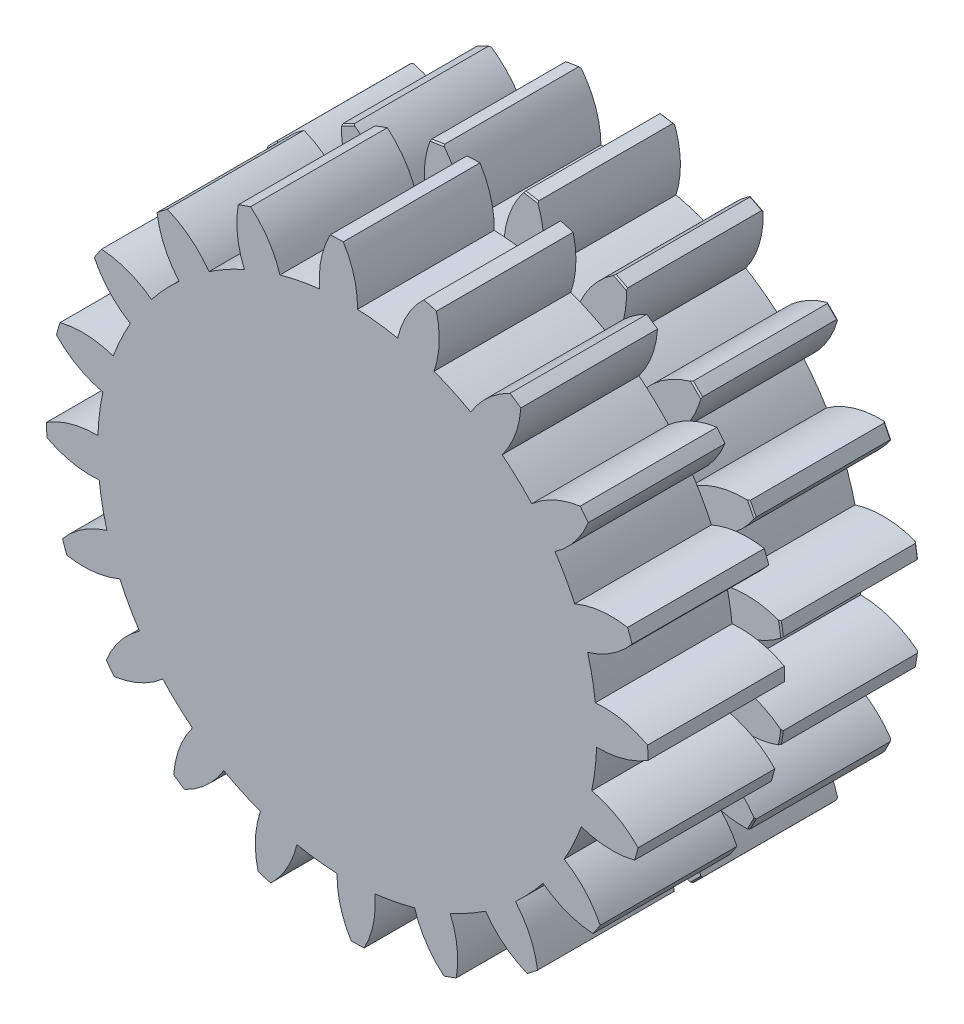
SolidWorks part; units mm, degrees
ref_plane "Front Plane" through (0, 0, 0) normal (0, 0, 1) x (1, 0, 0)
ref_plane "Top Plane" through (0, 0, 0) normal (0, 1, 0) x (1, 0, 0)
ref_plane "Right Plane" through (0, 0, 0) normal (1, 0, 0) x (0, 0, -1)
sketch "Sketch2" plane through (0, 0, 0) normal (0, 0, 1) x (1, 0, 0)
  circle A0 centre (0, 0) radius 20 construction
  circle A1 centre (0, 0) radius 22
  dimension "pitch cirlcle" = 40
  dimension "pitch circle 2" = 44
extrude "Boss-Extrude1" add sketch "Sketch2" along normal mid plane 10
sketch "Sketch3" plane through (0, 0, 5) normal (0, 0, 1) x (1, 0, 0)
  line L0 (0, 0) -> (0, 22) construction
  line L1 (6.7984, 20.9232) -> (0, 0) construction
  line L2 (0, 0) -> (3.4416, 21.7291) construction
  line L3 (0, 0) -> (-1.1551, 17.9629) construction
  line L4 (-1.5692, 19.9383) -> (1.5692, 19.9383) construction
  line L5 (1.5692, 19.9383) -> (4.6689, 19.4474) construction
  line L6 (0, 15.6271) -> (-2.2766, 21.8819) construction
  arc A0 (1.1551, 17.9629) -> (-1.1551, 17.9629) centre (0, 0) ccw
  circle A2 centre (0, 0) radius 22 construction
  circle A3 centre (0, 0) radius 19.75 construction
  arc A4 (-2.6166, 21.8438) -> (-1.1551, 17.9629) centre (-8.2502, 17.5067) cw
  arc A5 (2.6166, 21.8438) -> (1.1551, 17.9629) centre (8.2502, 17.5067) ccw
  circle A6 centre (0, 0) radius 20 construction
  circle A7 centre (0, 0) radius 22 construction
  arc A8 (2.6166, 21.8438) -> (-2.6166, 21.8438) centre (0, 0) ccw
  dimension "angle displacement" = 18
  dimension "dedenum" = 4
  dimension "addendum" = 2.25
  dimension "Pressure Angle" = 20
extrude "Cut-Extrude1" cut sketch "Sketch3" against normal blind 10
fillet "Fillet1" radius 0.6 2 edges at (1.1551, 17.9629, 0) (-1.1551, 17.9629, 0)
chamfer "Chamfer1" distance 0.1 2 edges at (0, -22, -5) (0, -22, 5)
pattern_circular "CirPattern1" count 20 over 360 about axis through (0, 0, 0) along (0, 0, 1) of "Cut-Extrude1", "Fillet1"
sketch "Sketch6" plane through (0, 0, 5) normal (0, 0, 1) x (1, 0, 0)
  line L0 (-2.969, 21.7987) -> (-2.3981, 24.057)
  line L1 (-2.3981, 24.057) -> (2.7785, 23.6602)
  line L2 (2.7785, 23.6602) -> (2.969, 21.7987)
  arc A0 (-1.445, 17.5517) -> (-2.969, 21.7987) centre (-8.2502, 17.5067) ccw
  arc A1 (2.969, 21.7987) -> (1.445, 17.5517) centre (8.2502, 17.5067) ccw
  arc A2 (-2.5466, 21.7514) -> (-2.6166, 21.8438) centre (-8.2502, 17.5067) ccw construction
  arc A3 (2.6166, 21.8438) -> (2.5466, 21.7514) centre (8.2502, 17.5067) ccw construction
  arc A4 (-2.6166, 21.8438) -> (-4.2616, 21.5833) centre (0, 0) ccw construction
  arc A5 (4.2616, 21.5833) -> (2.6166, 21.8438) centre (0, 0) ccw construction
  arc A7 (1.445, 17.5517) -> (-1.445, 17.5517) centre (0, 0) ccw
extrude "Cut-Extrude3" cut sketch "Sketch6" against normal through all
pattern_circular "CirPattern2" count 20 over 360 about axis through (0, 0, 0) along (0, 0, 1) of "Cut-Extrude3"
ref_point "Point1"
sketch "Sketch8" plane through (0, 0, 5) normal (0, 0, 1) x (1, 0, 0)
  circle A1 centre (0, 0) radius 22
extrude "Boss-Extrude2" add sketch "Sketch8" along normal blind 10
sketch "Sketch9" plane through (0, 0, 15) normal (0, 0, 1) x (1, 0, 0)
  line L0 (-8.2502, 17.5067) -> (0, 0) construction
  line L1 (0, 0) -> (-6.0551, 18.3816) construction
  line L2 (10.3222, 16.3707) -> (0, 0) construction
  line L3 (8.2502, 17.5067) -> (0, 0) construction
  arc A0 (1.0529, 18.2269) -> (0.065, 21.9999) centre (-6.0551, 18.3816) ccw
  arc A1 (5.2592, 21.3621) -> (3.3878, 17.9402) centre (10.3222, 16.3707) ccw
  arc A2 (-1.1551, 17.9629) -> (-2.6166, 21.8438) centre (-8.2502, 17.5067) ccw construction
  arc A3 (2.6166, 21.8438) -> (1.1551, 17.9629) centre (8.2502, 17.5067) ccw construction
  circle A5 centre (0, 0) radius 19.3533 construction
  arc A6 (3.3878, 17.9402) -> (1.0529, 18.2269) centre (0, 0) ccw
  arc A7 (21.0387, 6.4322) -> (0.065, 21.9999) centre (0, 0) ccw
  arc A8 (2.6166, 21.8438) -> (-2.6166, 21.8438) centre (0, 0) ccw construction
  arc A10 (21.0387, 6.4322) -> (0.065, 21.9999) centre (0, 0) ccw
  arc A11 (21.0387, 6.4322) -> (0.065, 21.9999) centre (0, 0) ccw
  circle M9 centre (0, 0) radius 22
  dimension "D1" = 7
  dimension "D2" = 7
extrude "Cut-Extrude4" cut sketch "Sketch9" against normal blind 10 contours A6 A1 A0 M9
pattern_circular "CirPattern3" count 20 over 360 about axis through (0, 0, 0) along (0, 0, 1) of "Cut-Extrude4"
sketch "Sketch10" plane through (0, 0, 15) normal (0, 0, 1) x (1, 0, 0)
  arc A6 (0.7488, 18.2419) -> (-0.2903, 21.9981) centre (-6.0551, 18.3816) ccw
  arc A7 (3.6866, 17.8812) -> (0.7488, 18.2419) centre (0, 0) ccw
  arc A8 (5.6035, 21.2744) -> (-0.2903, 21.9981) centre (0, 0) ccw
  arc A9 (5.6035, 21.2744) -> (3.6866, 17.8812) centre (10.3222, 16.3707) ccw
extrude "Cut-Extrude5" cut sketch "Sketch10" against normal blind 10
pattern_circular "CirPattern4" count 20 over 360 about axis through (0, 0, 0) along (0, 0, 1) of "Cut-Extrude5"
equation "\"module\"= 2mm"
equation "\"number of teeth\"= 20"
equation "\"pressure angle\"= 20"
equation "\"pitch cirlcle@Sketch2\"= \"module\" * \"number of teeth\""
equation "\"pitch circle 2@Sketch2\"= \"module\" * ( \"number of teeth\" + 2 )"
equation "\"angle displacement@Sketch3\"= 360 / \"number of teeth\""
equation "\"addendum@Sketch3\"= IIF ( \"module\" >= 1.25 , 2.25 , 2.4 )"
equation "\"Pressure Angle@Sketch3\"= \"pressure angle\""
equation "\"D1@CirPattern1\"= \"number of teeth\""
equation "\"D1@Fillet1\"= 0.3 * \"module\""
equation "\"D1@CirPattern2\"=\"number of teeth\""
equation "\"D1@CirPattern3\"=\"number of teeth\""
